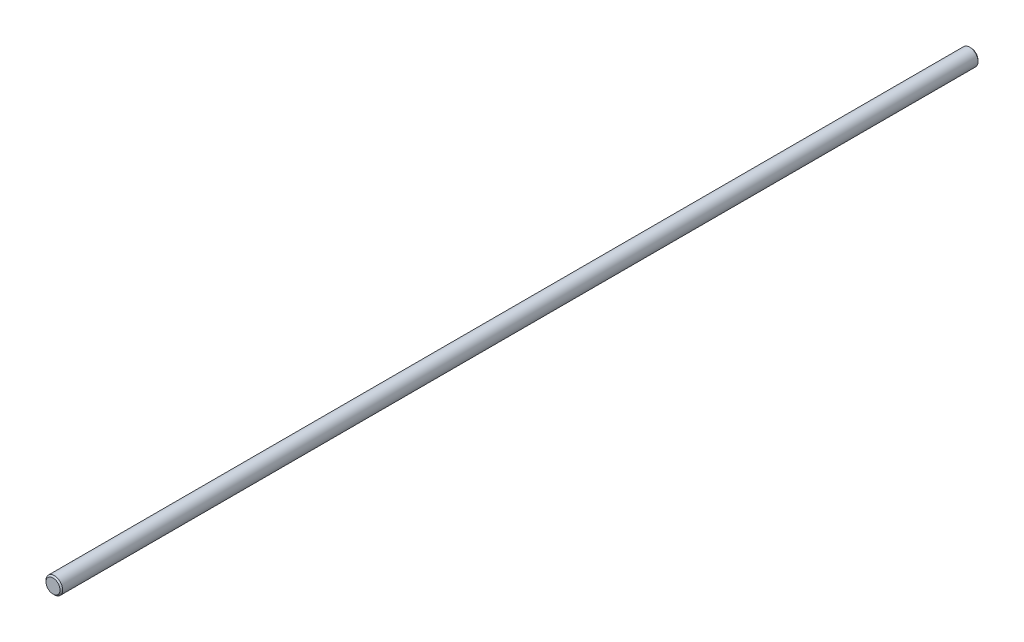
SolidWorks part; units mm, degrees
ref_plane "Front Plane" through (0, 0, 0) normal (0, 0, 1) x (1, 0, 0)
ref_plane "Top Plane" through (0, 0, 0) normal (0, 1, 0) x (1, 0, 0)
ref_plane "Right Plane" through (0, 0, 0) normal (1, 0, 0) x (0, 0, -1)
sketch "Sketch1" plane through (0, 0, 0) normal (0, 0, 1) x (1, 0, 0)
  circle A0 centre (0, 0) radius 3.175
  dimension "D1" = 6.35
extrude "Boss-Extrude1" add sketch "Sketch1" along normal blind 349.25
chamfer "Chamfer1" distance 0.508 angle 45 2 edges at (3.175, 0, 0) (3.175, 0, 349.25)
